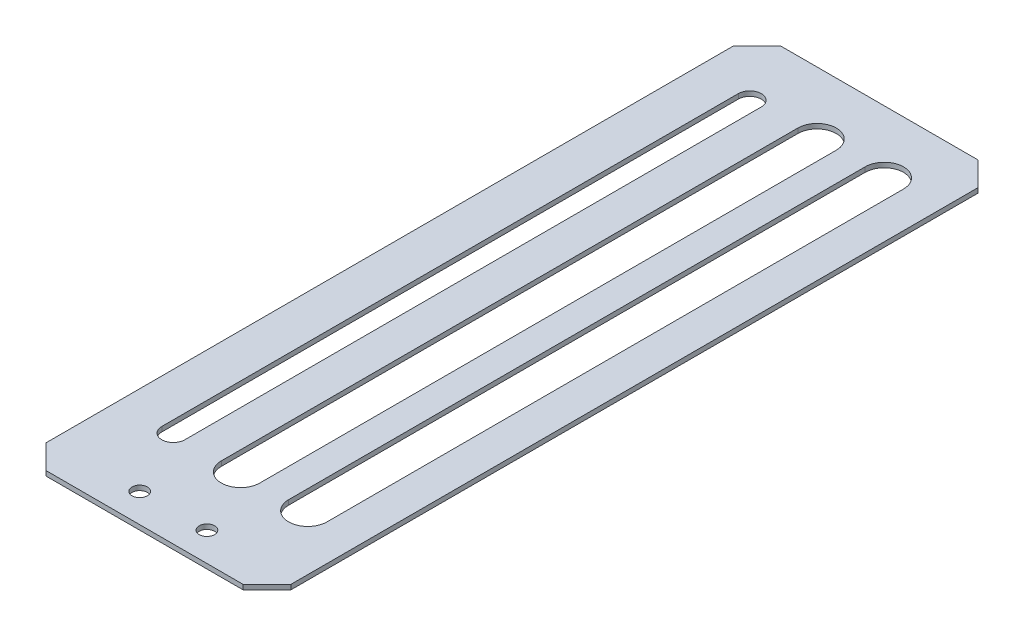
SolidWorks part; units mm, degrees
material "Hexcel AS4C (3000 丝)"
ref_plane "前视基准面" through (0, 0, 0) normal (0, 0, 1) x (1, 0, 0)
ref_plane "上视基准面" through (0, 0, 0) normal (0, 1, 0) x (1, 0, 0)
ref_plane "右视基准面" through (0, 0, 0) normal (1, 0, 0) x (0, 0, -1)
sketch "草图1" plane through (0, 0, 0) normal (0, 1, 0) x (1, 0, 0)
  line L1 (25.5, 76.5) -> (-25.5, 76.5)
  line L2 (25.5, 76.5) -> (25.5, -76.5)
  line L3 (25.5, -76.5) -> (-25.5, -76.5)
  line L4 (-25.5, 76.5) -> (-25.5, -76.5)
  line L5 (25.5, 76.5) -> (-25.5, -76.5) construction
  line L6 (25.5, -76.5) -> (-25.5, 76.5) construction
  point P0 (0, 0)
  dimension "D1" = 153
  dimension "D2" = 51
extrude "凸台-拉伸1" add sketch "草图1" along normal blind 1
sketch "草图2" plane through (0, 1, 0) normal (0, 1, 0) x (1, 0, 0)
  line L0 (-7, -70.5) -> (7, -70.5) construction
  line L1 (-25.5, -76.5) -> (25.5, -76.5) construction
  line L2 (-14, 63.5) -> (-14, -56.5) construction
  line L3 (-10, 63.5) -> (-10, -56.5)
  line L4 (-18, 63.5) -> (-18, -56.5)
  line L5 (0, 63.5) -> (0, -56.5) construction
  line L6 (4, 63.5) -> (4, -56.5)
  line L7 (-4, 63.5) -> (-4, -56.5)
  line L8 (14, 63.5) -> (14, -56.5) construction
  line L9 (18, 63.5) -> (18, -56.5)
  line L10 (10, 63.5) -> (10, -56.5)
  circle A0 centre (-7, -70.5) radius 1.6
  circle A1 centre (7, -70.5) radius 1.6
  arc A2 (-10, 63.5) -> (-18, 63.5) centre (-14, 63.5) ccw
  arc A3 (-18, -56.5) -> (-10, -56.5) centre (-14, -56.5) ccw
  arc A4 (4, 63.5) -> (-4, 63.5) centre (0, 63.5) ccw
  arc A5 (-4, -56.5) -> (4, -56.5) centre (0, -56.5) ccw
  arc A6 (18, 63.5) -> (10, 63.5) centre (14, 63.5) ccw
  arc A7 (10, -56.5) -> (18, -56.5) centre (14, -56.5) ccw
  point P4 (0, -70.5)
  point P10 (-14, 3.5)
  point P18 (0, 3.5)
  point P26 (14, 3.5)
  dimension "D1" = 3.2
  dimension "D4" = 4
  dimension "D6" = 20
  dimension "D2" = 14
  dimension "D3" = 6
  dimension "D5" = 120
  dimension "D8" = 6
  dimension "D7" = 3
extrude "切除-拉伸1" cut sketch "草图2" against normal through all
chamfer "倒角1" distance 5 angle 45 4 edges at (-25.5, 0.5, -76.5) (25.5, 0.5, -76.5) (25.5, 0.5, 76.5) (-25.5, 0.5, 76.5)
sketch "草图3" plane through (0, 1, 0) normal (0, 1, 0) x (1, 0, 0)
  line L0 (-24, 0) -> (-50024, 0) construction
  line L1 (-25.5, 71.5) -> (-25.5, -71.5) construction
  line L2 (0, 0) -> (0, -50000) construction
  line L4 (8, -30) -> (-8, -30) construction
  circle A2 centre (-8, -30) radius 1.35
  circle A4 centre (-19.75, 26) radius 1.3
  point P4 (-25.5, 0)
  point P8 (-21, 0)
  point P11 (2.1981, 0)
  point P12 (0, -30)
  dimension "D3" = 2.7
  dimension "D4" = 2.6
  dimension "D1" = 30
  dimension "D2" = 16
  dimension "D5" = 56
  dimension "D6" = 11.75
extrude "切除-拉伸2" [suppressed] cut sketch "草图3" against normal through all
sketch "草图4" plane through (0, 1, 0) normal (0, 1, 0) x (1, 0, 0)
  line L0 (-10, -56.5) -> (-10, 63.5) construction
  line L1 (-18, 63.5) -> (-18, -56.5) construction
  line L2 (-10, -56.5) -> (-10, 63.5)
  line L3 (-18, 63.5) -> (-18, -56.5)
  line L4 (-14, 63.5) -> (-14, -56.5) construction
  line L5 (-11.6, 63.5) -> (-11.6, -56.5)
  line L6 (-16.4, 63.5) -> (-16.4, -56.5)
  arc A0 (-18, -56.5) -> (-10, -56.5) centre (-14, -56.5) ccw construction
  arc A1 (-10, 63.5) -> (-18, 63.5) centre (-14, 63.5) ccw construction
  arc A2 (-18, -56.5) -> (-10, -56.5) centre (-14, -56.5) ccw
  arc A3 (-10, 63.5) -> (-18, 63.5) centre (-14, 63.5) ccw
  arc A4 (-11.6, 63.5) -> (-16.4, 63.5) centre (-14, 63.5) ccw
  arc A5 (-16.4, -56.5) -> (-11.6, -56.5) centre (-14, -56.5) ccw
  point P3 (-14, 3.5)
  dimension "D1" = 2.4
extrude "凸台-拉伸2" add sketch "草图4" against normal blind 1
